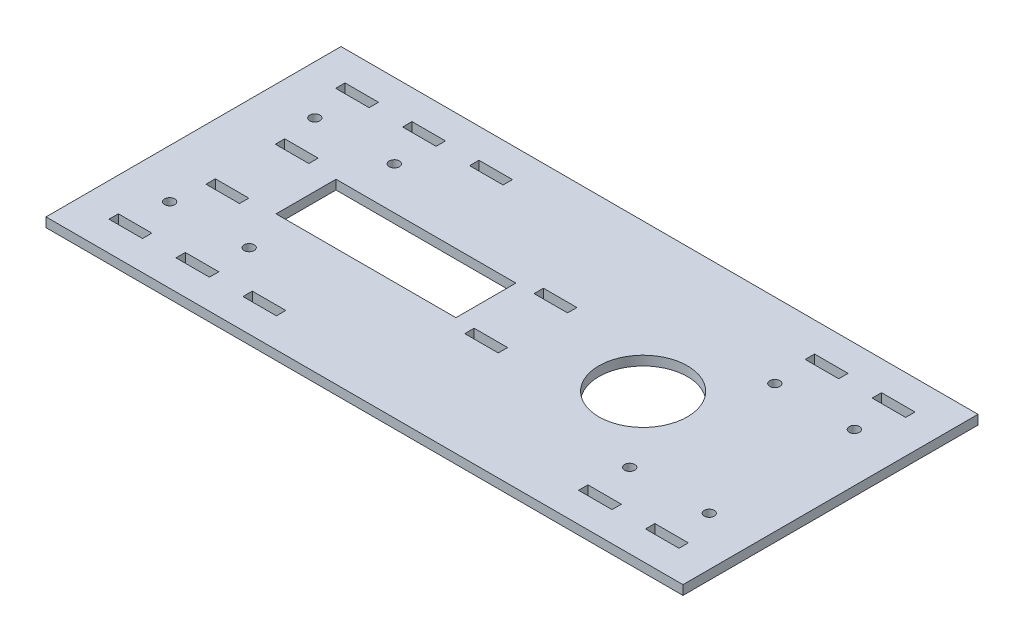
SolidWorks part; units mm, degrees
ref_plane "Front Plane" through (0, 0, 0) normal (0, 0, 1) x (1, 0, 0)
ref_plane "Top Plane" through (0, 0, 0) normal (0, 1, 0) x (1, 0, 0)
ref_plane "Right Plane" through (0, 0, 0) normal (1, 0, 0) x (0, 0, -1)
sketch "Sketch1" plane through (0, 0, 0) normal (0, 1, 0) x (1, 0, 0)
  line L1 (-109.2058, 67.4639) -> (106.6942, 67.4639)
  line L2 (-109.2058, 67.4639) -> (-109.2058, -32.5361)
  line L3 (-109.2058, -32.5361) -> (106.6942, -32.5361)
  line L4 (106.6942, 67.4639) -> (106.6942, -32.5361)
  dimension "D1" = 100
  dimension "D2" = 215.9
extrude "Boss-Extrude1" add sketch "Sketch1" along normal blind 3.175
sketch "Sketch3" plane through (0, 3.175, 0) normal (0, 1, 0) x (1, 0, 0)
  line L0 (106.6942, 67.4639) -> (-109.2058, 67.4639) construction
  line L1 (-97.8558, 57.4639) -> (-86.5058, 57.4639)
  line L2 (-97.8558, 57.4639) -> (-97.8558, 54.2889)
  line L3 (-97.8558, 54.2889) -> (-86.5058, 54.2889)
  line L4 (-86.5058, 57.4639) -> (-86.5058, 54.2889)
  line L5 (-109.2058, 67.4639) -> (-109.2058, -32.5361) construction
  line L6 (-52.4558, 57.4639) -> (-41.1058, 57.4639)
  line L7 (-75.1558, 57.4639) -> (-63.8058, 57.4639)
  line L8 (-75.1558, 57.4639) -> (-75.1558, 54.2889)
  line L9 (-75.1558, 54.2889) -> (-63.8058, 54.2889)
  line L10 (-63.8058, 57.4639) -> (-63.8058, 54.2889)
  line L11 (-52.4558, 57.4639) -> (-52.4558, 54.2889)
  line L12 (-52.4558, 54.2889) -> (-41.1058, 54.2889)
  line L13 (-41.1058, 57.4639) -> (-41.1058, 54.2889)
  line L14 (61.2942, 57.4639) -> (72.6442, 57.4639)
  line L15 (61.2942, 57.4639) -> (61.2942, 54.2889)
  line L16 (61.2942, 54.2889) -> (72.6442, 54.2889)
  line L17 (72.6442, 57.4639) -> (72.6442, 54.2889)
  line L18 (106.6942, -32.5361) -> (106.6942, 67.4639) construction
  line L19 (83.9942, 57.4639) -> (95.3442, 57.4639)
  line L20 (83.9942, 57.4639) -> (83.9942, 54.2889)
  line L21 (83.9942, 54.2889) -> (95.3442, 54.2889)
  line L22 (95.3442, 57.4639) -> (95.3442, 54.2889)
  point P26 (72.6442, 55.8764)
  point P27 (83.9942, 55.8764)
  dimension "D1" = 10
  dimension "D2" = 11.35
  dimension "D3" = 11.35
  dimension "D4" = 11.35
  dimension "D5" = 11.35
  dimension "D6" = 3.175
  dimension "D7" = 11.35
  dimension "D8" = 11.35
  dimension "D9" = 11.35
  dimension "D10" = 3.175
  dimension "D11" = 11.35
  dimension "D12" = 11.35
extrude "Cut-Extrude2" cut sketch "Sketch3" against normal blind 3.175
sketch "Sketch4" plane through (0, 3.175, 0) normal (0, 1, 0) x (1, 0, 0)
  line L0 (-109.2058, -32.5361) -> (106.6942, -32.5361) construction
  line L1 (-97.8558, -19.3611) -> (-86.5058, -19.3611)
  line L2 (-97.8558, -19.3611) -> (-97.8558, -22.5361)
  line L3 (-97.8558, -22.5361) -> (-86.5058, -22.5361)
  line L4 (-86.5058, -19.3611) -> (-86.5058, -22.5361)
  line L5 (-109.2058, 67.4639) -> (-109.2058, -32.5361) construction
  line L6 (106.6942, -32.5361) -> (106.6942, 67.4639) construction
  line L7 (-75.1558, -19.3611) -> (-63.8058, -19.3611)
  line L8 (-75.1558, -19.3611) -> (-75.1558, -22.5361)
  line L9 (-75.1558, -22.5361) -> (-63.8058, -22.5361)
  line L10 (-63.8058, -19.3611) -> (-63.8058, -22.5361)
  line L11 (-52.4558, -19.3611) -> (-41.1058, -19.3611)
  line L12 (-52.4558, -19.3611) -> (-52.4558, -22.5361)
  line L13 (-52.4558, -22.5361) -> (-41.1058, -22.5361)
  line L14 (-41.1058, -19.3611) -> (-41.1058, -22.5361)
  line L15 (61.2942, -19.3611) -> (72.6442, -19.3611)
  line L16 (61.2942, -19.3611) -> (61.2942, -22.5361)
  line L17 (61.2942, -22.5361) -> (72.6442, -22.5361)
  line L18 (72.6442, -19.3611) -> (72.6442, -22.5361)
  line L19 (83.9942, -19.3611) -> (95.3442, -19.3611)
  line L20 (83.9942, -19.3611) -> (83.9942, -22.5361)
  line L21 (83.9942, -22.5361) -> (95.3442, -22.5361)
  line L22 (95.3442, -19.3611) -> (95.3442, -22.5361)
  point P6 (-97.8558, -20.9486)
  dimension "D1" = 10
  dimension "D2" = 11.35
  dimension "D3" = 11.35
  dimension "D4" = 3.175
  dimension "D5" = 11.35
  dimension "D6" = 11.35
  dimension "D7" = 11.35
  dimension "D8" = 11.35
  dimension "D9" = 11.35
  dimension "D10" = 11.35
  dimension "D11" = 11.35
  dimension "D12" = 11.35
extrude "Cut-Extrude3" cut sketch "Sketch4" against normal blind 3.175
sketch "Sketch5" plane through (0, 3.175, 0) normal (0, 1, 0) x (1, 0, 0)
  line L0 (-109.2058, 67.4639) -> (-109.2058, -32.5361) construction
  line L1 (-71.1058, 27.6639) -> (-10.1458, 27.6639)
  line L2 (-71.1058, 27.6639) -> (-71.1058, 7.3439)
  line L3 (-71.1058, 7.3439) -> (-10.1458, 7.3439)
  line L4 (-10.1458, 27.6639) -> (-10.1458, 7.3439)
  line L7 (106.6942, 67.4639) -> (-109.2058, 67.4639) construction
  dimension "D1" = 38.1
  dimension "D2" = 20.32
  dimension "D3" = 39.8
extrude "Cut-Extrude4" cut sketch "Sketch5" against normal blind 3.175 and the other way through all
sketch "Sketch6" plane through (0, 3.175, 0) normal (0, 1, 0) x (1, 0, 0)
  line L0 (-109.2058, -32.5361) -> (106.6942, -32.5361) construction
  line L1 (106.6942, 67.4639) -> (-109.2058, 67.4639) construction
  line L2 (-109.2058, 67.4639) -> (-109.2058, -32.5361) construction
  line L3 (106.6942, -32.5361) -> (106.6942, 67.4639) construction
  circle A0 centre (-92.6958, 42.0639) radius 1.7145
  circle A1 centre (-65.7464, 42.0639) radius 1.7145
  circle A2 centre (-92.6958, -7.1361) radius 1.7145
  circle A3 centre (-65.7464, -7.1361) radius 1.7145
  circle A4 centre (63.2348, 42.0639) radius 1.7145
  circle A5 centre (90.1842, 42.0639) radius 1.7145
  circle A6 centre (63.2348, -7.1361) radius 1.7145
  circle A7 centre (90.1842, -7.1361) radius 1.7145
  dimension "D1" = 26.9494
  dimension "D2" = 26.9494
  dimension "D3" = 25.4
  dimension "D4" = 25.4
  dimension "D5" = 16.51
  dimension "D6" = 26.9494
  dimension "D7" = 25.4
  dimension "D8" = 25.4
  dimension "D9" = 16.51
  dimension "D10" = 128.9812
extrude "Cut-Extrude5" cut sketch "Sketch6" against normal blind 3.175
sketch "Sketch7" plane through (0, 3.175, 0) normal (0, 1, 0) x (1, 0, 0)
  line L0 (106.6942, 67.4639) -> (-109.2058, 67.4639) construction
  line L1 (106.6942, -32.5361) -> (106.6942, 67.4639) construction
  circle A0 centre (43.1942, 17.4639) radius 15
  dimension "D1" = 50
  dimension "D2" = 63.5
extrude "Cut-Extrude6" cut sketch "Sketch7" against normal blind 3.175
sketch "Sketch8" plane through (0, 3.175, 0) normal (0, 1, 0) x (1, 0, 0)
  line L0 (-91.6798, 7.3439) -> (-80.3298, 7.3439)
  line L1 (-91.6798, 7.3439) -> (-91.6798, 4.1689)
  line L2 (-91.6798, 4.1689) -> (-80.3298, 4.1689)
  line L3 (-80.3298, 7.3439) -> (-80.3298, 4.1689)
  line L4 (-10.1458, 7.3439) -> (-71.1058, 7.3439) construction
  line L5 (-91.6798, 30.8389) -> (-80.3298, 30.8389)
  line L6 (-91.6798, 30.8389) -> (-91.6798, 27.6639)
  line L7 (-91.6798, 27.6639) -> (-80.3298, 27.6639)
  line L8 (-80.3298, 30.8389) -> (-80.3298, 27.6639)
  line L9 (-71.1058, 27.6639) -> (-10.1458, 27.6639) construction
  line L10 (-3.9698, 7.3439) -> (7.3802, 7.3439)
  line L11 (-3.9698, 7.3439) -> (-3.9698, 4.1689)
  line L12 (-3.9698, 4.1689) -> (7.3802, 4.1689)
  line L13 (7.3802, 7.3439) -> (7.3802, 4.1689)
  line L14 (-3.9698, 30.8389) -> (7.3802, 30.8389)
  line L15 (-3.9698, 30.8389) -> (-3.9698, 27.6639)
  line L16 (-3.9698, 27.6639) -> (7.3802, 27.6639)
  line L17 (7.3802, 30.8389) -> (7.3802, 27.6639)
  line L18 (-71.1058, 7.3439) -> (-10.1458, 7.3439) construction
  line L19 (-10.1458, 27.6639) -> (-71.1058, 27.6639) construction
  line L20 (-109.2058, 67.4639) -> (-109.2058, -32.5361) construction
  dimension "D1" = 11.35
  dimension "D2" = 11.35
  dimension "D3" = 11.35
  dimension "D4" = 99.06
  dimension "D5" = 17.526
extrude "Cut-Extrude7" cut sketch "Sketch8" against normal blind 3.175
